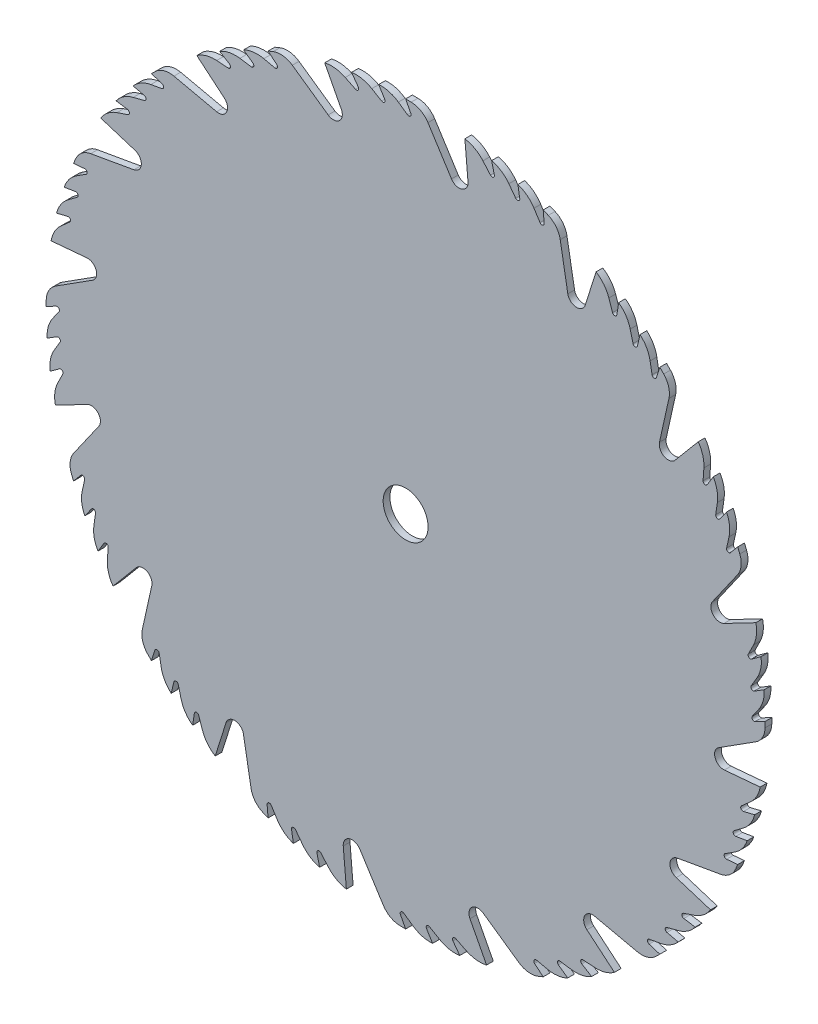
SolidWorks part; units mm, degrees
ref_plane "Front Plane" through (0, 0, 0) normal (0, 0, 1) x (1, 0, 0)
ref_plane "Top Plane" through (0, 0, 0) normal (0, 1, 0) x (1, 0, 0)
ref_plane "Right Plane" through (0, 0, 0) normal (1, 0, 0) x (0, 0, -1)
sketch "Sketch1" plane through (0, 0, 0) normal (0, 0, 1) x (1, 0, 0)
  circle A0 centre (0, 0) radius 127
  circle A1 centre (0, 0) radius 7.9375
  dimension "D1" = 254
  dimension "D2" = 15.875
extrude "Extrude1" add sketch "Sketch1" along normal blind 2.3813
sketch "Sketch2" plane through (0, 0, 2.3813) normal (0, 0, 1) x (1, 0, 0)
  line L0 (0, 0) -> (0, 127) construction
  line L1 (0, 127) -> (1.8326, 123.4797)
  line L2 (0.6732, 122.463) -> (-2.5684, 124.7327)
  line L3 (1.8326, 123.4797) -> (0, 123.4797) construction
  line L4 (0.6732, 122.463) -> (0, 122.463) construction
  line L5 (-9.525, 126.6423) -> (-7.3834, 123.1884)
  line L6 (-8.4632, 122.0876) -> (-11.9496, 124.1576)
  line L7 (-19.1154, 125.5532) -> (-16.7176, 122.2719)
  line L8 (-17.7107, 121.0923) -> (-21.3443, 122.8915)
  line L9 (-9.525, 126.6423) -> (0, 0) construction
  line L10 (-7.3834, 123.1884) -> (-9.2546, 123.0476) construction
  line L11 (-8.4632, 122.0876) -> (-9.1784, 122.0338) construction
  line L12 (-19.1154, 125.5532) -> (0, 0) construction
  line L13 (-16.7176, 122.2719) -> (-18.5728, 121.9894) construction
  line L14 (-17.7107, 121.0923) -> (-18.4197, 120.9843) construction
  line L15 (-28.5953, 123.7389) -> (-22.7311, 112.4738)
  line L16 (-27.3685, 108.407) -> (-40.0379, 117.2782)
  line L17 (0, 0) -> (-28.5953, 123.7389) construction
  line L18 (-25.5474, 111.0078) -> (-25.6532, 111.0078) construction
  line L19 (-27.3685, 108.407) -> (-25.0522, 108.407) construction
  line L20 (-27.3685, 108.407) -> (-35.1015, 108.407) construction
  circle A0 centre (0, 0) radius 127 construction
  arc A1 (1.8326, 123.4797) -> (0.6732, 122.463) centre (1.1285, 123.1132) cw
  arc A2 (-2.5684, 124.7327) -> (-9.525, 126.6423) centre (-8.7205, 115.9465) ccw
  arc A3 (-7.3834, 123.1884) -> (-8.4632, 122.0876) centre (-8.058, 122.7701) cw
  arc A4 (-11.9496, 124.1576) -> (-19.1154, 125.5532) centre (-17.4838, 114.8366) ccw
  arc A5 (-16.7176, 122.2719) -> (-17.7107, 121.0923) centre (-17.3585, 121.8036) cw
  arc A6 (-21.3443, 122.8915) -> (-28.5953, 123.7389) centre (-26.1546, 113.1772) ccw
  arc A7 (-22.7311, 112.4738) -> (-27.3685, 108.407) centre (-25.5474, 111.0078) cw
  arc A8 (-40.0379, 117.2782) -> (-46.7822, 118.0696) centre (-44.1447, 111.4131) ccw
  arc A9 (-46.7822, 118.0696) -> (0, 127) centre (0, 0) cw
  circle M1 centre (0, 0) radius 127
  dimension "D3" = 0.7937
  dimension "D7" = 0.7937
  dimension "D9" = 0.7937
  dimension "D11" = 4.064
  dimension "D14" = 62.5
  dimension "D16" = 3.175
  dimension "D1" = 3.9688
  dimension "D2" = 62.5
  dimension "D4" = 35
  dimension "D5" = 9.525
  dimension "D6" = 4.064
  dimension "D8" = 9.652
  dimension "D10" = 9.652
  dimension "D12" = 62.5
  dimension "D13" = 35
  dimension "D15" = 35
  dimension "D17" = 62.5
  dimension "D18" = 12.7
  dimension "D19" = 35
  dimension "D20" = 19.05
extrude "Extrude2" cut sketch "Sketch2" against normal through all contours A8 L16 A7 L15 M1 | A6 L8 A5 L7 M1 | A4 L6 A3 L5 M1 | A2 L2 A1 L1 M1
pattern_circular "CirPattern1" count 16 every 22.5 about axis through (0, 0, 0) along (0, 0, 1) of "Extrude2"
